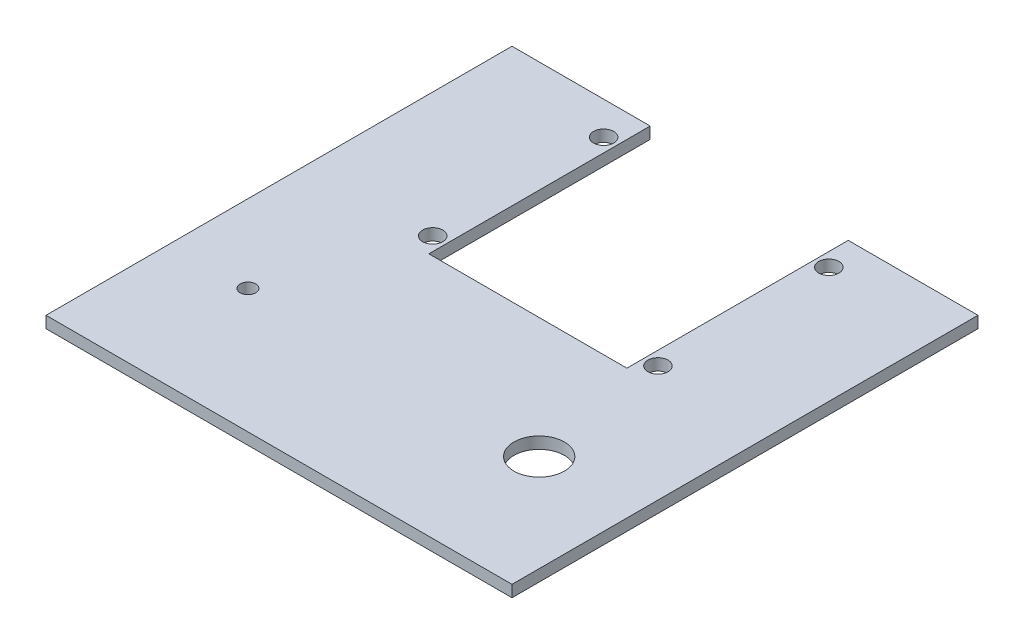
SolidWorks part; units mm, degrees
ref_plane "前视基准面" through (0, 0, 0) normal (0, 0, 1) x (1, 0, 0)
ref_plane "上视基准面" through (0, 0, 0) normal (0, 1, 0) x (1, 0, 0)
ref_plane "右视基准面" through (0, 0, 0) normal (1, 0, 0) x (0, 0, -1)
sketch "草图1" plane through (0, 0, 0) normal (0, 1, 0) x (1, 0, 0)
  line L0 (0, 0) -> (120, 0)
  line L1 (120, 0) -> (120, -120)
  line L2 (120, -120) -> (0, -120)
  line L4 (0, -120) -> (0, 0)
extrude "凸台-拉伸1" add sketch "草图1" along normal blind 3
sketch "草图2" plane through (0, 3, 0) normal (0, 1, 0) x (1, 0, 0)
  line L0 (35.5866, 0) -> (86.5866, 0)
  line L1 (86.5866, 0) -> (86.5866, -57)
  line L2 (86.5866, -57) -> (35.5866, -57)
  line L3 (35.5866, -57) -> (35.5866, 0)
  line L4 (0, -120) -> (120, -120) construction
  line L5 (120, -120) -> (120, 0) construction
  line L6 (0, 0) -> (0, -120) construction
  line L7 (120, 0) -> (0, 0) construction
  circle A0 centre (20, -88) radius 2
  circle A1 centre (95, -88) radius 6.5
  circle A2 centre (32.0866, -8.5) radius 2.6
  circle A3 centre (32.0866, -52.5) radius 2.6
  circle A4 centre (90.0866, -8.5) radius 2.6
  circle A5 centre (90.0866, -52.5) radius 2.6
  dimension "D1" = 32
  dimension "D4" = 20
  dimension "D5" = 58
  dimension "D6" = 3.5
  dimension "D7" = 44
  dimension "D8" = 44
  dimension "D9" = 58
  dimension "D10" = 3.5
  dimension "D12" = 8.5
  dimension "D2" = 32
  dimension "D3" = 25
  dimension "D11" = 8.5
extrude "切除-拉伸1" cut sketch "草图2" against normal blind 3
